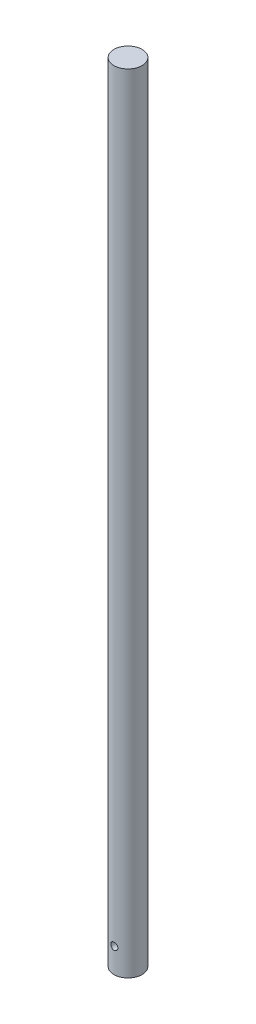
SolidWorks part; units mm, degrees
ref_plane "Front Plane" through (0, 0, 0) normal (0, 0, 1) x (1, 0, 0)
ref_plane "Top Plane" through (0, 0, 0) normal (0, 1, 0) x (1, 0, 0)
ref_plane "Right Plane" through (0, 0, 0) normal (1, 0, 0) x (0, 0, -1)
sketch "Sketch1" plane through (0, 0, 0) normal (0, 1, 0) x (1, 0, 0)
  circle A0 centre (0, 0) radius 6.35
  dimension "D1" = 12.7
extrude "Boss-Extrude1" add sketch "Sketch1" along normal mid plane 355.6
sketch "Sketch2" plane through (0, 0, 0) normal (0, 0, 1) x (1, 0, 0)
  line L0 (-6.35, -177.8) -> (6.35, -177.8) construction
  circle A0 centre (0, -166.6875) radius 1.5875
  dimension "D1" = 3.175
  dimension "D2" = 11.1125
extrude "Cut-Extrude1" cut sketch "Sketch2" along normal through all both and the other way through all
equation "\".f\"=0.902734"
equation "\"0.90273378i.5\"=0.902734"
